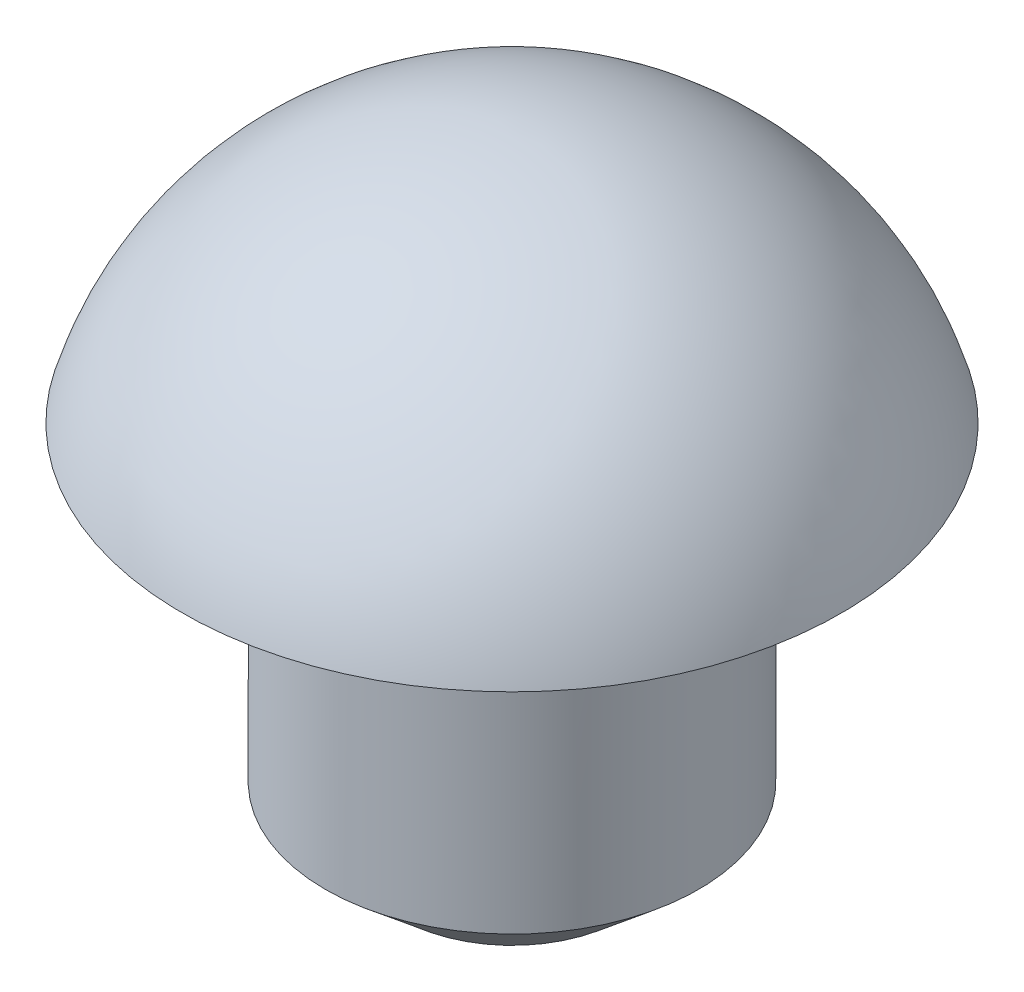
SolidWorks part; units mm, degrees
ref_plane "Ebene vorne" through (0, 0, 0) normal (0, 0, 1) x (1, 0, 0)
ref_plane "Ebene oben" through (0, 0, 0) normal (0, 1, 0) x (1, 0, 0)
ref_plane "Ebene rechts" through (0, 0, 0) normal (1, 0, 0) x (0, 0, -1)
ref_axis "Achse1" through (0, -7.4577, 0) along (0, 1, 0)
sketch "Skizze1" plane through (0, 0, 0) normal (0, 0, 1) x (1, 0, 0)
  line L0 (0, -55) -> (0, 55) construction
  line L1 (-2.65, -2.5) -> (0, -2.5)
  line L2 (-2.65, -2.5) -> (-2.65, 2.5)
  line L3 (-2.65, 2.5) -> (0, 2.5)
  line L4 (0, -2.5) -> (0, 2.5)
  line L5 (-2.65, -2.5) -> (0, 2.5) construction
  line L6 (-2.65, 2.5) -> (0, -2.5) construction
  point P0 (-1.325, 0)
  dimension "D1" = 5
  dimension "D2" = 2.65
revolve "Rotation1" add sketch "Skizze1" angle 360 about axis through (0, -7.4577, 0) along (0, 1, 0)
sketch "Skizze2" plane through (0, 0, 0) normal (0, 0, 1) x (1, 0, 0)
  line L0 (0, -7.4577) -> (0, 9.0063) construction
  line L1 (-2.65, -2.5) -> (-1.5, -2.5)
  line L2 (-2.65, -2.5) -> (-2.65, 0.5)
  line L3 (-2.65, 0.5) -> (-1.5, 0.5)
  line L4 (-1.5, -2.5) -> (-1.5, 0.5)
  line L5 (2.65, 2.5) -> (-2.65, 2.5) construction
  dimension "D1" = 1.5
  dimension "D2" = 2
revolve "Schnitt-Rotation1" cut sketch "Skizze2" angle 360 about axis through (0, -7.4577, 0) along (0, 1, 0)
sketch "Skizze3" plane through (0, 0, 0) normal (0, 0, 1) x (1, 0, 0)
  line L0 (0, -7.4577) -> (0, 9.0063) construction
  line L1 (2.65, 2.5) -> (-2.65, 2.5) construction
  line L2 (-2.65, 0.5) -> (-4.3918, 0.5)
  line L3 (-4.3918, 0.5) -> (-4.3918, 3.8899)
  line L4 (-4.3918, 3.8899) -> (0, 3.8899)
  line L5 (0, 3.8899) -> (0, 2.5)
  arc A0 (0, 2.5) -> (-2.65, 0.5) centre (0, -0.2556) ccw
revolve "Schnitt-Rotation2" cut sketch "Skizze3" angle 360 about axis through (0, -7.4577, 0) along (0, 1, 0)
chamfer "Fase1" distance 0.5 angle 50 1 edges at (0, -2.5, -1.5)
